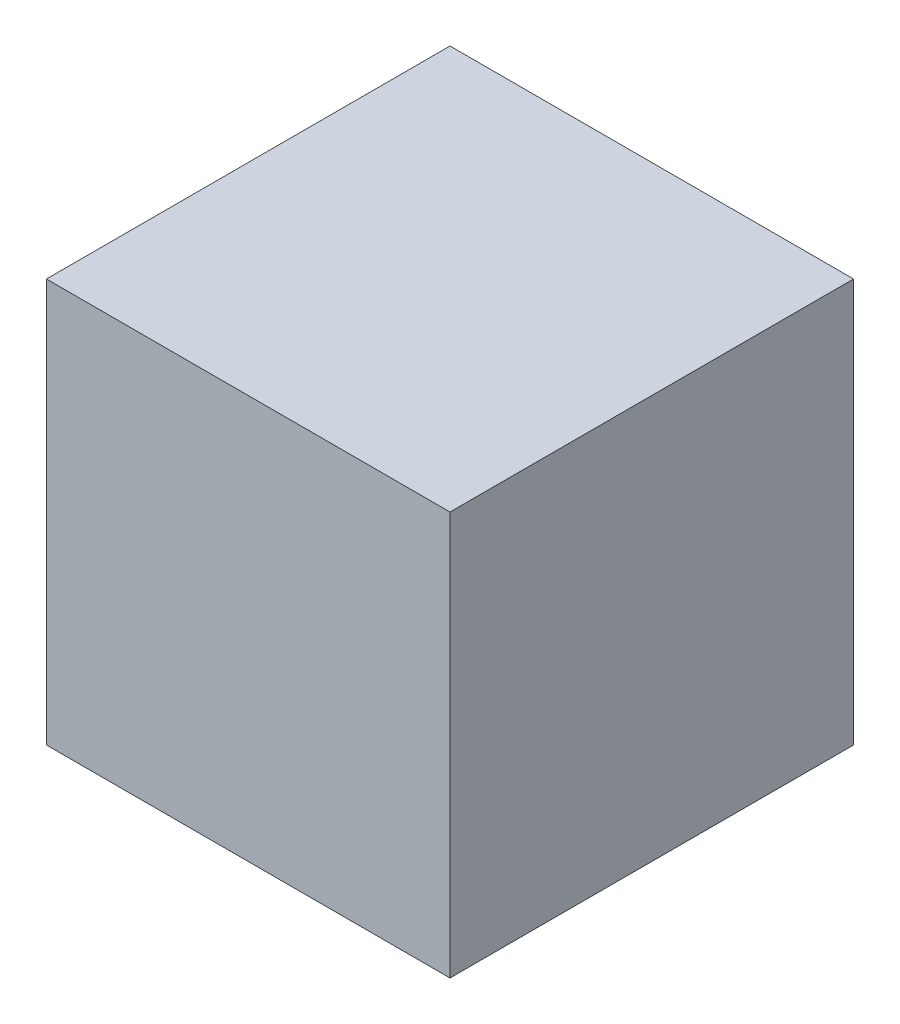
SolidWorks part; units mm, degrees
ref_plane "Front" through (0, 0, 0) normal (0, 0, 1) x (1, 0, 0)
ref_plane "Top" through (0, 0, 0) normal (0, 1, 0) x (1, 0, 0)
ref_plane "Right" through (0, 0, 0) normal (1, 0, 0) x (0, 0, -1)
sketch "Sketch1" plane through (0, 0, 0) normal (0, 1, 0) x (1, 0, 0)
  line L1 (-28.829, 28.829) -> (28.829, 28.829)
  line L2 (-28.829, 28.829) -> (-28.829, -28.829)
  line L3 (-28.829, -28.829) -> (28.829, -28.829)
  line L4 (28.829, 28.829) -> (28.829, -28.829)
  line L5 (-28.829, 28.829) -> (28.829, -28.829) construction
  line L6 (-28.829, -28.829) -> (28.829, 28.829) construction
  point P0 (0, 0)
  dimension "D1" = 57.658
  dimension "D2" = 57.658
extrude "Boss-Extrude1" add sketch "Sketch1" along normal blind 57.658
